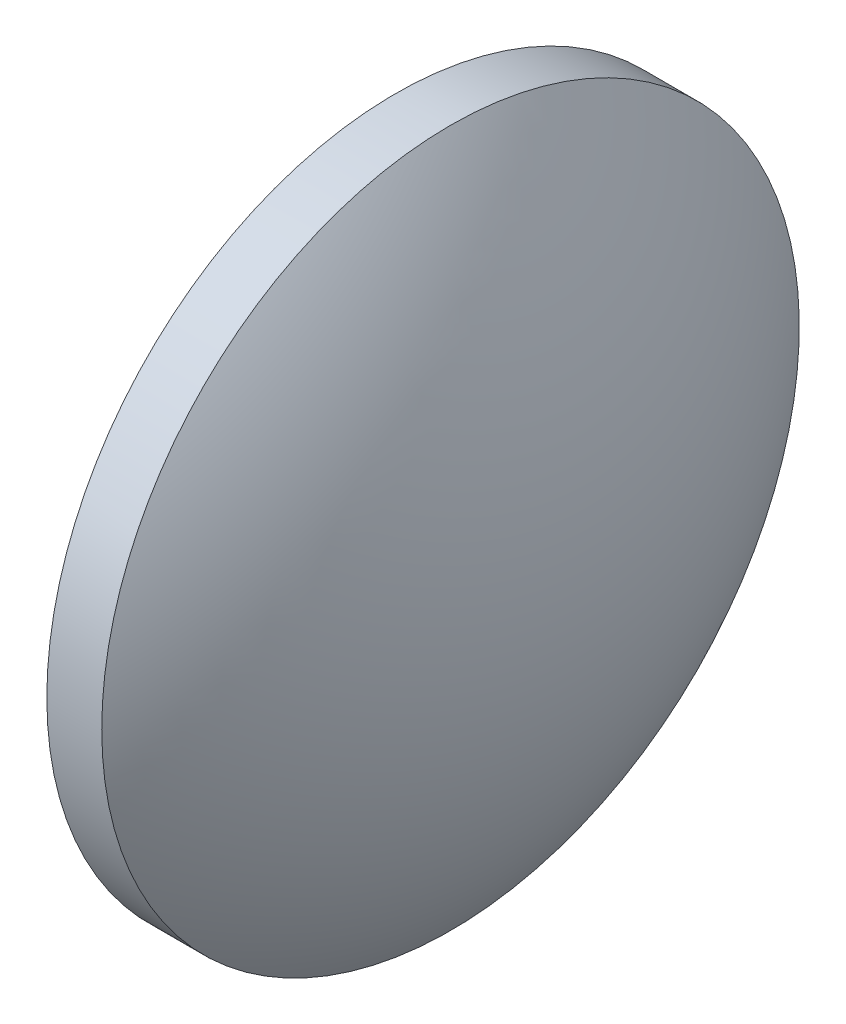
SolidWorks part; units mm, degrees
ref_plane "前视基准面" through (0, 0, 0) normal (0, 0, 1) x (1, 0, 0)
ref_plane "上视基准面" through (0, 0, 0) normal (0, 1, 0) x (1, 0, 0)
ref_plane "右视基准面" through (0, 0, 0) normal (1, 0, 0) x (0, 0, -1)
sketch "草图1" plane through (0, 0, 0) normal (0, 0, 1) x (1, 0, 0)
  line L0 (673.6721, 68.0362) -> (692.4681, 68.0362) construction
  line L1 (679.4103, 68.0362) -> (679.4103, 80.7362)
  line L2 (679.4103, 80.7362) -> (681.4103, 80.7362)
  line L3 (685.5103, 68.0362) -> (679.4103, 68.0362)
  arc A0 (685.5103, 68.0362) -> (681.4103, 80.7362) centre (663.7908, 68.0362) ccw
revolve "旋转1" add sketch "草图1" angle 360 about L0
